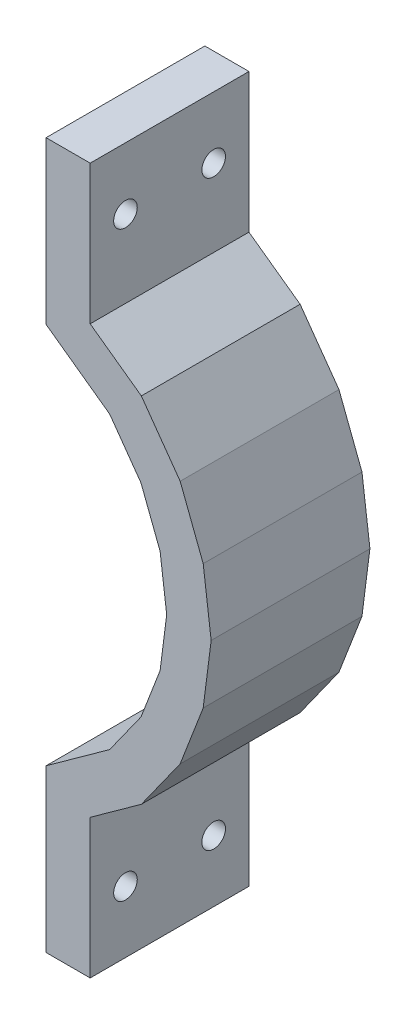
SolidWorks part; units mm, degrees
ref_plane "Front Plane" through (0, 0, 0) normal (0, 0, 1) x (1, 0, 0)
ref_plane "Top Plane" through (0, 0, 0) normal (0, 1, 0) x (1, 0, 0)
ref_plane "Right Plane" through (0, 0, 0) normal (1, 0, 0) x (0, 0, -1)
sketch "Model" plane through (0, 0, 0) normal (0, 0, 1) x (1, 0, 0)
  line L0 (-43.8688, -5.5181) -> (-25.5343, -5.5181) construction
  line L42 (35.3595, 21.9963) -> (44.5131, 15.4007)
  line L43 (44.5131, 15.4007) -> (49.0274, 9.0714)
  line L44 (49.0274, 9.0714) -> (51.7777, 1.9175)
  line L45 (51.7777, 1.9175) -> (52.7242, -5.5181)
  line L46 (51.7777, -12.9538) -> (52.7242, -5.5181)
  line L47 (49.0274, -20.1076) -> (51.7777, -12.9538)
  line L48 (44.5131, -26.437) -> (49.0274, -20.1076)
  line L49 (35.3595, -33.0325) -> (44.5131, -26.437)
  line L71 (41.7095, 25.2475) -> (41.7095, 45.2819)
  line L77 (52.7242, -5.5181) -> (1077.4342, -5.5181) construction
  line L94 (41.7095, 25.2475) -> (49.0748, 19.9405)
  line L95 (35.3595, -56.3181) -> (41.7095, -56.3181)
  line L96 (49.0748, 19.9405) -> (54.6652, 12.1024)
  line L97 (54.6652, 12.1024) -> (57.9801, 3.4802)
  line L98 (57.9801, 3.4802) -> (59.1254, -5.5181)
  line L99 (57.9801, -14.5165) -> (59.1254, -5.5181)
  line L100 (54.6652, -23.1387) -> (57.9801, -14.5165)
  line L101 (49.0748, -30.9767) -> (54.6652, -23.1387)
  line L102 (41.7095, -36.2838) -> (49.0748, -30.9767)
  line L106 (35.3595, 45.2819) -> (41.7095, 45.2819)
  line L107 (41.7095, -56.3181) -> (41.7095, -36.2838)
  line L108 (35.3595, 45.2819) -> (35.3595, 21.9963)
  line L109 (35.3595, -33.0325) -> (35.3595, -56.3181)
  dimension "D2" = 101.6
  dimension "D4" = 44.5131
  dimension "D5" = 49.0274
  dimension "D6" = 49.0748
  dimension "D7" = 51.7777
  dimension "D8" = 52.7242
  dimension "D9" = 54.6652
  dimension "D10" = 57.9801
  dimension "D11" = 59.1254
  dimension "D12" = 6.35
  dimension "D13" = 35.3595
  dimension "D14" = 1.9175
  dimension "D15" = 25.2475
  dimension "D36" = 3.4802
  dimension "D40" = 9.0714
  dimension "D43" = 12.1024
  dimension "D49" = 15.4007
  dimension "D54" = 19.9405
  dimension "D57" = 21.9963
  dimension "D63" = 5.5181
extrude "Boss-Extrude1" add sketch "Model" along normal blind 22.86
hole_wizard "M3 Clearance Hole1" positions "Sketch1" profile "Sketch2" hole size "M3" standard "ANSI Metric" end condition through all
sketch "Sketch1" plane through (41.7095, 0, 0) normal (1, 0, 0) x (0, 0, -1)
  line L0 (-22.86, -56.3181) -> (0, -56.3181) construction
  line L1 (-22.86, -56.3181) -> (-22.86, -36.2838) construction
  line L3 (-22.86, 45.2819) -> (0, 45.2819) construction
  line L5 (0, 25.2475) -> (0, 45.2819) construction
  point P0 (-17.78, 36.3919)
  point P2 (-5.08, 36.3919)
  point P4 (-17.78, -47.4281)
  point P6 (-5.08, -47.4281)
  dimension "D1" = 8.89
  dimension "D2" = 8.89
  dimension "D3" = 12.7
  dimension "D4" = 5.08
  dimension "D5" = 8.89
  dimension "D6" = 8.89
  dimension "D7" = 5.08
  dimension "D8" = 12.7
sketch "Sketch2" plane through (41.7095, 36.3919, 17.78) normal (0, 1, 0) x (0, 0, -1)
  line L0 (0, 0) -> (0, 6.35)
  line L1 (0, 6.35) -> (1.7, 6.35)
  line L2 (1.7, 6.35) -> (1.7, 0)
  line L5 (1.7, 0) -> (0, 0)
  line L11 (0, -6.35) -> (0, 107.95) construction
  dimension "Thru Hole Dia." = 3.4
  dimension "Thru Hole Depth" = 6.35
